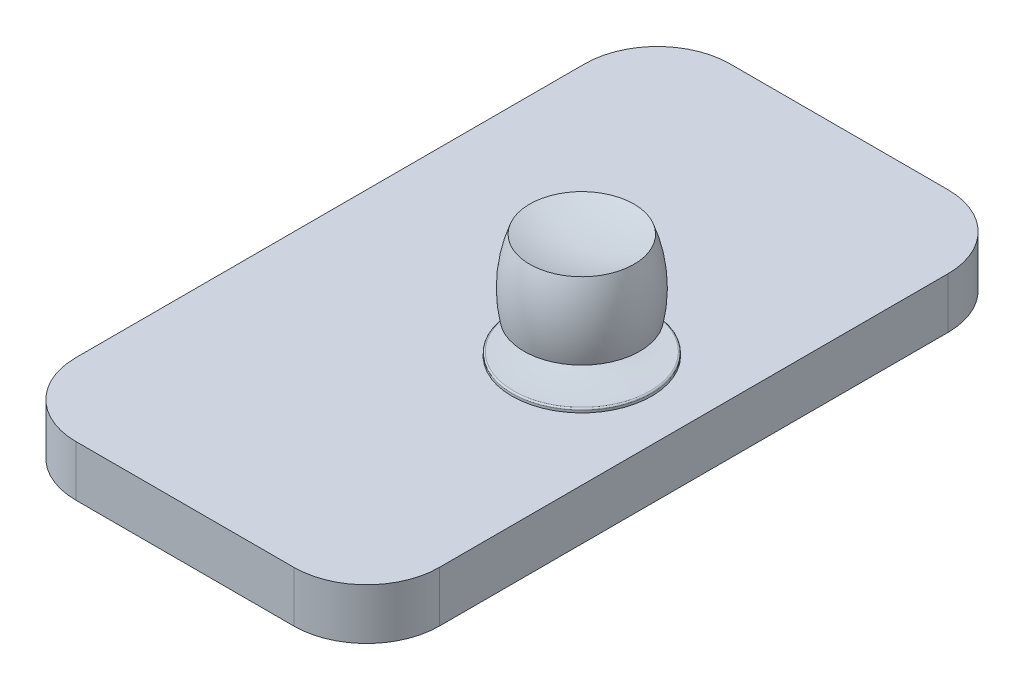
SolidWorks part; units mm, degrees
ref_plane "Front Plane" through (0, 0, 0) normal (0, 0, 1) x (1, 0, 0)
ref_plane "Top Plane" through (0, 0, 0) normal (0, 1, 0) x (1, 0, 0)
ref_plane "Right Plane" through (0, 0, 0) normal (1, 0, 0) x (0, 0, -1)
sketch "Sketch1" plane through (0, 0, 0) normal (0, 1, 0) x (1, 0, 0)
  line L1 (-63.5, 114.3) -> (63.5, 114.3)
  line L2 (-63.5, 114.3) -> (-63.5, -114.3)
  line L3 (-63.5, -114.3) -> (63.5, -114.3)
  line L4 (63.5, 114.3) -> (63.5, -114.3)
  line L5 (-63.5, 114.3) -> (63.5, -114.3) construction
  line L6 (-63.5, -114.3) -> (63.5, 114.3) construction
  point P0 (0, 0)
  dimension "D1" = 127
  dimension "D2" = 228.6
extrude "Boss-Extrude1" add sketch "Sketch1" along normal blind 17.78
fillet "Fillet1" radius 25.4 4 edges at (-63.5, 8.89, 114.3) (-63.5, 8.89, -114.3) (63.5, 8.89, -114.3) (63.5, 8.89, 114.3)
sketch "Sketch3" plane through (0, 0, 0) normal (0, 0, 1) x (1, 0, 0)
  line L1 (24.4007, 17.78) -> (0, 17.78)
  line L2 (18.3194, 23.8314) -> (18.3194, 20.4537)
  line L4 (0, 17.78) -> (0, 18.6211)
  line L5 (24.4007, 21.7325) -> (24.4007, 17.78)
  line L6 (24.4007, 17.78) -> (22.5217, 17.78)
  line L7 (18.3194, 23.8314) -> (18.3194, 27.9405)
  line L8 (18.3194, 27.9405) -> (24.4007, 27.9405)
  line L9 (24.4007, 23.8314) -> (24.4007, 21.7325)
  line L10 (24.4007, 27.9405) -> (24.4007, 23.8314)
  arc A0 (0.5204, 19.1289) -> (18.3194, 20.4537) centre (2.7279, 109.7015) ccw
  arc A1 (0.5204, 19.1289) -> (0, 18.6211) centre (0.508, 18.6211) ccw
  dimension "D1" = 0.508
revolve "Revolve1" add sketch "Sketch3" angle 360 about L5
sketch "Sketch4" plane through (0, 0, 0) normal (0, 0, 1) x (1, 0, 0)
  line L0 (30.482, 27.9405) -> (18.3194, 27.9405) construction
  line L2 (24.4007, 27.9405) -> (24.4007, 52.1025)
  arc A0 (42.6305, 54.63) -> (24.4007, 52.1025) centre (25.0593, 114.3581) cw
  arc A1 (42.6305, 54.63) -> (44.6463, 29.3031) centre (-1.3285, 38.3875) cw
  arc A2 (24.4007, 27.9405) -> (44.6463, 29.3031) centre (30.908, 82.3385) ccw
revolve "Revolve2" add sketch "Sketch4" angle 360 about L2
